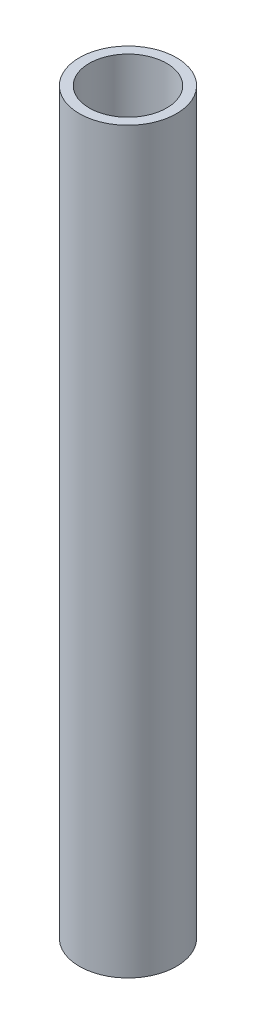
SolidWorks part; units mm, degrees
material "Plain Carbon Steel"
ref_plane "Front Plane" through (0, 0, 0) normal (0, 0, 1) x (1, 0, 0)
ref_plane "Top Plane" through (0, 0, 0) normal (0, 1, 0) x (1, 0, 0)
ref_plane "Right Plane" through (0, 0, 0) normal (1, 0, 0) x (0, 0, -1)
sketch "Sketch1" plane through (0, 0, 0) normal (0, 1, 0) x (1, 0, 0)
  circle A0 centre (0, 0) radius 16.7005
  circle A1 centre (0, 0) radius 13.3223
  dimension "D1" = 33.401
  dimension "D2" = 26.6446
extrude "Boss-Extrude1" add sketch "Sketch1" along normal blind 254
